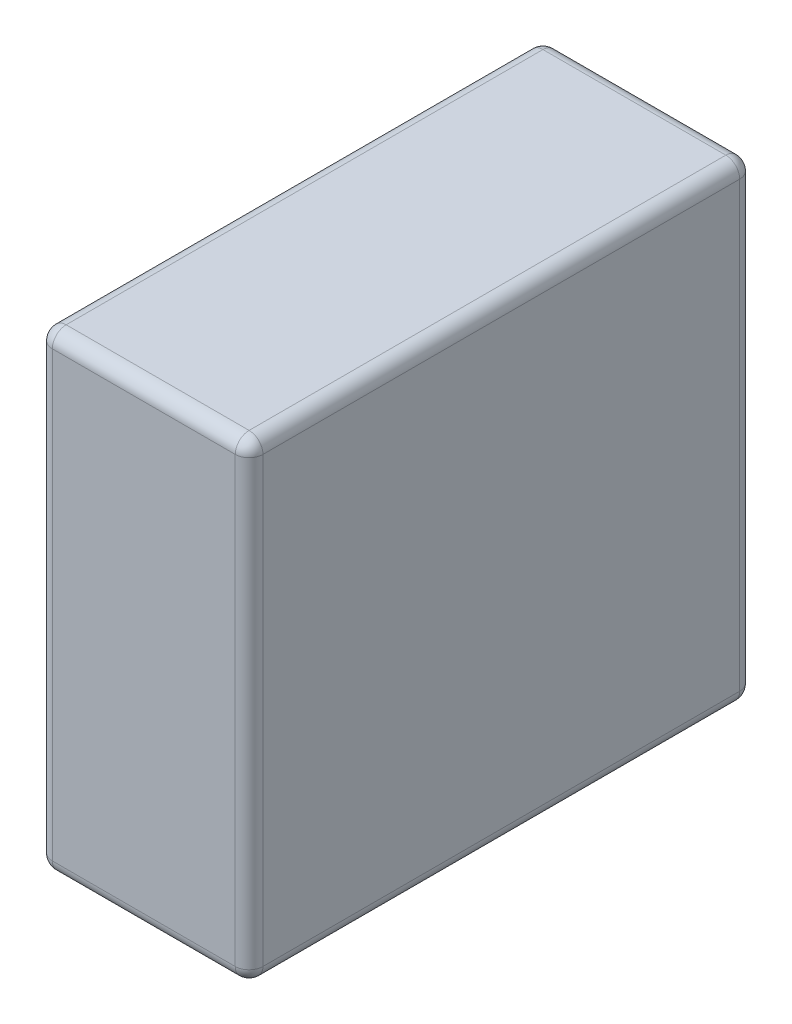
SolidWorks part; units mm, degrees
ref_plane "Спереди" through (0, 0, 0) normal (0, 0, 1) x (1, 0, 0)
ref_plane "Сверху" through (0, 0, 0) normal (0, 1, 0) x (1, 0, 0)
ref_plane "Справа" through (0, 0, 0) normal (1, 0, 0) x (0, 0, -1)
sketch "Эскиз1" plane through (0, 0, 0) normal (0, 1, 0) x (1, 0, 0)
  line L0 (0, 91) -> (0, -91) construction
  line L1 (-38, 91) -> (38, 91)
  line L2 (-38, 91) -> (-38, -91)
  line L3 (-38, -91) -> (38, -91)
  line L4 (38, 91) -> (38, -91)
  point P6 (0, 0)
  dimension "D1" = 76
  dimension "D2" = 182
extrude "Бобышка-Вытянуть1" add sketch "Эскиз1" along normal blind 170
fillet "Скругление1" radius 5 12 edges at (-38, 170, 0) (-38, 0, 0) (38, 170, 0) (38, 0, 0) (38, 85, -91) (0, 170, -91) (-38, 85, -91) (0, 0, -91) (0, 170, 91) (38, 85, 91) (0, 0, 91) (-38, 85, 91)
